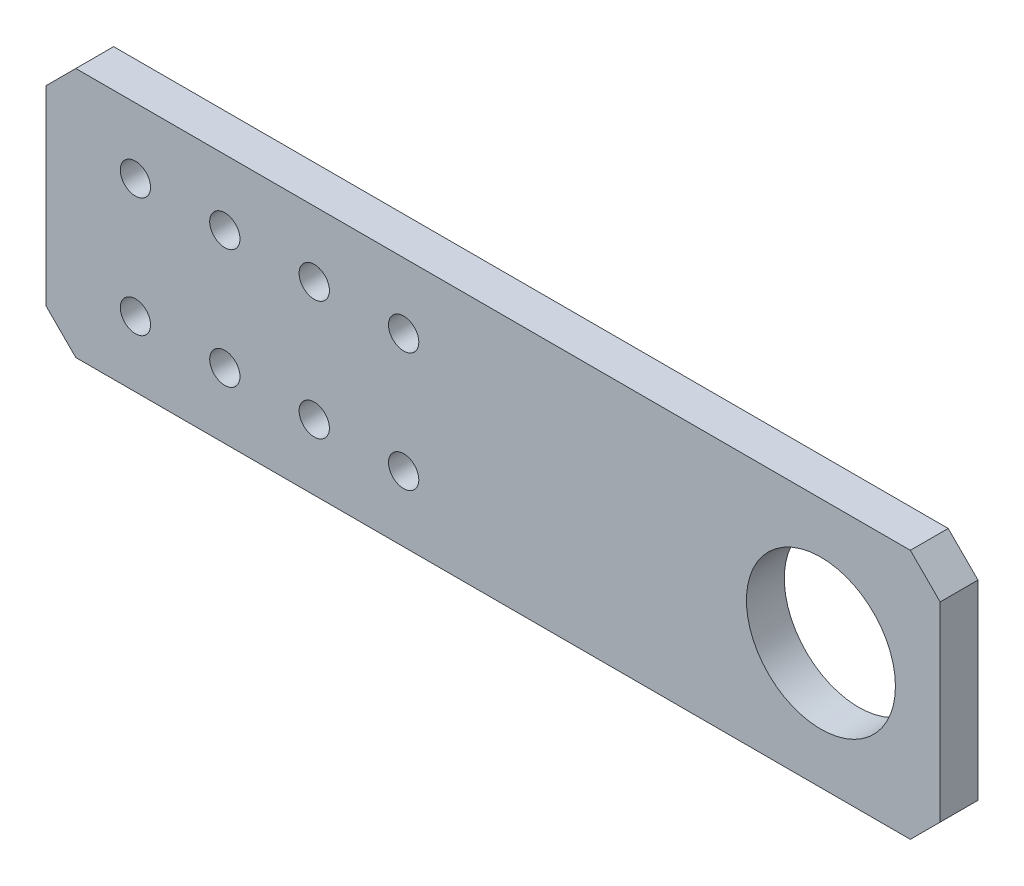
SolidWorks part; units mm, degrees
ref_plane "Front Plane" through (0, 0, 0) normal (0, 0, 1) x (1, 0, 0)
ref_plane "Top Plane" through (0, 0, 0) normal (0, 1, 0) x (1, 0, 0)
ref_plane "Right Plane" through (0, 0, 0) normal (1, 0, 0) x (0, 0, -1)
sketch "Sketch1" plane through (0, 0, 0) normal (0, 0, 1) x (1, 0, 0)
  line L1 (-100, 21) -> (100, 21)
  line L2 (-100, 21) -> (-100, -21)
  line L3 (-100, -21) -> (100, -21)
  line L4 (100, 21) -> (100, -21)
  line L5 (-100, 21) -> (100, -21) construction
  line L6 (-100, -21) -> (100, 21) construction
  point P0 (0, 0)
  dimension "D1" = 200
  dimension "D2" = 42
extrude "Boss-Extrude1" add sketch "Sketch1" along normal blind 6.35
sketch "Sketch3" plane through (0, 0, 6.35) normal (0, 0, 1) x (1, 0, 0)
  line L0 (-55, 10) -> (-55, -10) construction
  line L1 (-100, 21) -> (-100, -21) construction
  circle A0 centre (-55, 10) radius 2
  circle A1 centre (-55, -10) radius 2
  point P4 (-55, 0)
  dimension "D1" = 4
  dimension "D2" = 20
  dimension "D3" = 45
extrude "Cut-Extrude2" cut sketch "Sketch3" against normal through all
sketch "Sketch4" plane through (0, 0, 6.35) normal (0, 0, 1) x (1, 0, 0)
  line L0 (-100, 21) -> (-100, -21) construction
  line L1 (100, -21) -> (100, 21) construction
  circle A0 centre (-76, 0) radius 3.175
  circle A1 centre (80, 0) radius 3.175 construction
  dimension "D2" = 6.35
  dimension "D3" = 20
  dimension "D1" = 24
  dimension "D4" = 156
extrude "Cut-Extrude3" cut sketch "Sketch4" against normal through all
chamfer "Chamfer1" distance 5 angle 45 4 edges at (-100, 21, 3.175) (-100, -21, 3.175) (100, 21, 3.175) (100, -21, 3.175)
sketch "Sketch5" [suppressed] plane through (0, 0, 6.35) normal (0, 0, 1) x (1, 0, 0)
  line L0 (100, -16) -> (100, 16) construction
  circle A0 centre (77, 0) radius 11
  dimension "D1" = 22
  dimension "D2" = 23
extrude "Cut-Extrude4" [suppressed] cut sketch "Sketch5" against normal blind 25
sketch "Sketch7" [suppressed] plane through (0, 0, 6.35) normal (0, 0, 1) x (1, 0, 0)
  line L4 (7.5, 3.175) -> (-7.5, 3.175)
  line L5 (7.5, -3.175) -> (7.5, 3.175)
  line L6 (-7.5, -3.175) -> (7.5, -3.175)
  line L7 (-7.5, 3.175) -> (-7.5, -3.175)
  line L8 (7.5, 3.175) -> (-7.5, 3.175)
  line L9 (7.5, -3.175) -> (7.5, 3.175)
  line L10 (-7.5, -3.175) -> (7.5, -3.175)
  line L11 (-7.5, 3.175) -> (-7.5, -3.175)
  dimension "D1" = 0
extrude "Cut-Extrude6" [suppressed] cut sketch "Sketch7" against normal through all
sketch "Sketch8" [suppressed] plane through (0, 0, 6.35) normal (0, 0, 1) x (1, 0, 0)
  line L4 (25.5, 3.175) -> (10.5, 3.175)
  line L5 (10.5, 3.175) -> (10.5, -3.175)
  line L6 (10.5, -3.175) -> (25.5, -3.175)
  line L7 (25.5, -3.175) -> (25.5, 3.175)
  line L8 (25.5, 3.175) -> (10.5, 3.175)
  line L9 (10.5, 3.175) -> (10.5, -3.175)
  line L10 (10.5, -3.175) -> (25.5, -3.175)
  line L11 (25.5, -3.175) -> (25.5, 3.175)
  dimension "D1" = 0
extrude "Cut-Extrude7" [suppressed] cut sketch "Sketch8" against normal through all
sketch "Sketch9" plane through (0, 0, 6.35) normal (0, 0, 1) x (1, 0, 0)
  circle A0 centre (80, 0) radius 3.175 construction
  circle A1 centre (80, 0) radius 3.175
extrude "Cut-Extrude8" cut sketch "Sketch9" against normal through all
sketch "Sketch10" plane through (0, 0, 6.35) normal (0, 0, 1) x (1, 0, 0)
  circle A0 centre (80, 0) radius 12.5
  dimension "D1" = 25
extrude "Cut-Extrude9" cut sketch "Sketch10" against normal through all
sketch "Sketch11" [suppressed] plane through (0, 0, 6.35) normal (0, 0, 1) x (1, 0, 0)
  circle A0 centre (95.5563, 15.5563) radius 1.5 construction
  circle A1 centre (64.4437, 15.5563) radius 1.5 construction
  circle A2 centre (95.5563, -15.5563) radius 1.5 construction
  circle A3 centre (64.4437, -15.5563) radius 1.5 construction
  circle A4 centre (95.5563, 15.5563) radius 1.5
  circle A5 centre (64.4437, 15.5563) radius 1.5
  circle A6 centre (95.5563, -15.5563) radius 1.5
  circle A7 centre (64.4437, -15.5563) radius 1.5
extrude "Cut-Extrude10" [suppressed] cut sketch "Sketch11" against normal through all
sketch "Sketch12" plane through (0, 0, 6.35) normal (0, 0, 1) x (1, 0, 0)
  line L0 (-100, 16) -> (-100, -16) construction
  circle A0 centre (-93, 0) radius 3.302
  point P4 (-100, 0)
  dimension "D1" = 6.604
  dimension "D2" = 7
extrude "Cut-Extrude11" cut sketch "Sketch12" against normal through all
sketch "Sketch13" plane through (0, 0, 6.35) normal (0, 0, 1) x (1, 0, 0)
  line L0 (-50, 16) -> (-50, -16)
  line L1 (-45, 21) -> (-50, 16)
  line L2 (-50, -16) -> (-45, -21)
  line L3 (-95, -21) -> (95, -21) construction
  line L4 (95, 21) -> (-95, 21) construction
  line L5 (-95, -21) -> (95, -21)
  line L6 (95, 21) -> (-95, 21)
  line L8 (95, 21) -> (-95, 21)
  line L9 (-95, 21) -> (-100, 16)
  line L10 (-100, 16) -> (-100, -16)
  line L11 (-100, -16) -> (-95, -21)
  line L12 (-95, -21) -> (95, -21)
  line L13 (95, -21) -> (100, -16)
  line L14 (100, -16) -> (100, 16)
  line L15 (100, 16) -> (95, 21)
  line L16 (95, 21) -> (-45, 21)
  line L17 (-95, 21) -> (-100, 16)
  line L18 (-100, 16) -> (-100, -16)
  line L19 (-100, -16) -> (-95, -21)
  line L20 (-45, -21) -> (95, -21)
  line L21 (95, -21) -> (100, -16)
  line L22 (100, -16) -> (100, 16)
  line L23 (100, 16) -> (95, 21)
  line L26 (0, 0) -> (-50, 0) construction
  circle A4 centre (-35, 10) radius 2.54
  circle A5 centre (-20, 10) radius 2.54
  circle A6 centre (-5, 10) radius 2.54
  circle A7 centre (10, 10) radius 2.54
  circle A8 centre (-20, -10) radius 2.54
  circle A9 centre (-5, -10) radius 2.54
  circle A10 centre (10, -10) radius 2.54
  circle A11 centre (-35, -10) radius 2.54
  point P2 (-50, 21)
  point P9 (-50, -21)
  dimension "D8" = 4
  dimension "D3" = 15
  dimension "D7" = 5.08
  dimension "D2" = 150
  dimension "D4" = 10
  dimension "D1" = 0
  dimension "D9" = 2
extrude "Cut-Extrude12" cut sketch "Sketch13" against normal blind 10
